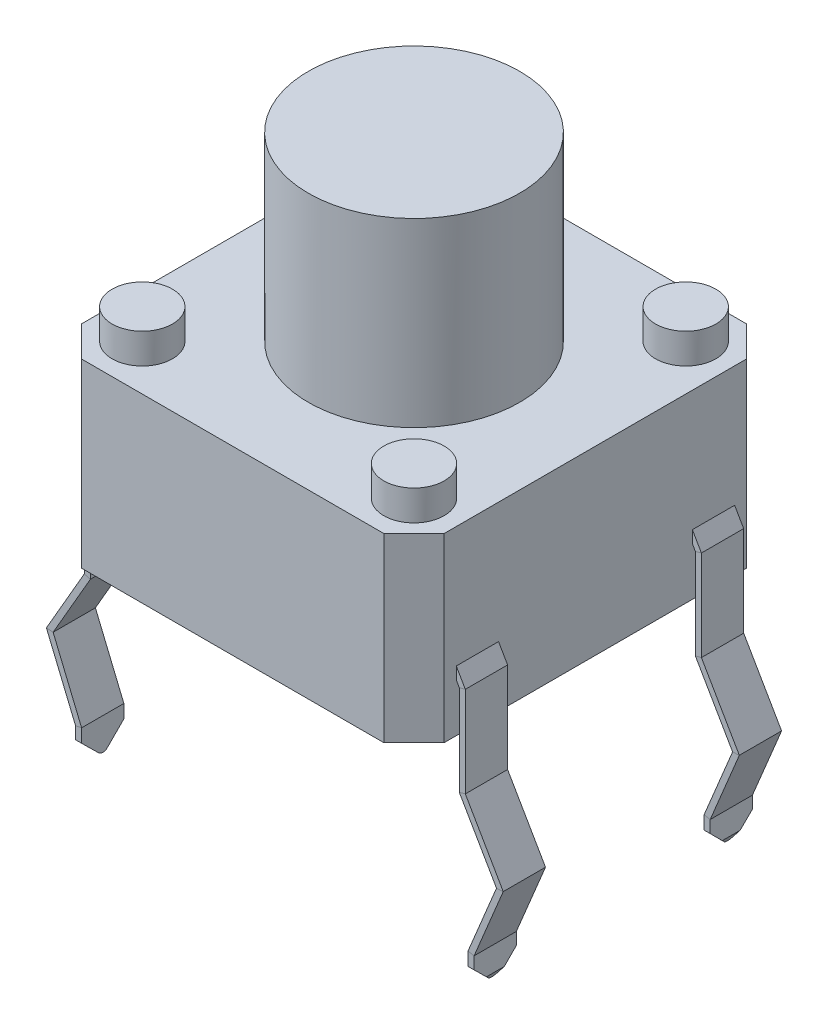
SolidWorks part; units mm, degrees
ref_plane "Front Plane" through (0, 0, 0) normal (0, 0, 1) x (1, 0, 0)
ref_plane "Top Plane" through (0, 0, 0) normal (0, 1, 0) x (1, 0, 0)
ref_plane "Right Plane" through (0, 0, 0) normal (1, 0, 0) x (0, 0, -1)
sketch "Sketch1" plane through (0, 0, 0) normal (0, 1, 0) x (1, 0, 0)
  line L1 (-3.005, -3.005) -> (3.005, -3.005)
  line L2 (-3.005, -3.005) -> (-3.005, 3.005)
  line L3 (-3.005, 3.005) -> (3.005, 3.005)
  line L4 (3.005, -3.005) -> (3.005, 3.005)
  line L5 (-3.005, -3.005) -> (3.005, 3.005) construction
  line L6 (-3.005, 3.005) -> (3.005, -3.005) construction
  point P0 (0, 0)
  dimension "D1" = 6.01
  dimension "D2" = 6.01
extrude "Boss-Extrude1" add sketch "Sketch1" along normal blind 3
chamfer "Chamfer1" distance 0.5 angle 45 4 edges at (3.005, 1.5, -3.005) (-3.005, 1.5, -3.005) (-3.005, 1.5, 3.005) (3.005, 1.5, 3.005)
sketch "Sketch3" plane through (0, 3, 0) normal (0, 1, 0) x (1, 0, 0)
  circle A0 centre (0, 0) radius 1.75
extrude "Boss-Extrude2" add sketch "Sketch3" along normal blind 3
sketch "Sketch4" plane through (0, 3, 0) normal (0, 1, 0) x (1, 0, 0)
  circle A0 centre (2.25, 2.25) radius 0.5
  circle A1 centre (2.25, -2.25) radius 0.5
  circle A2 centre (-2.25, 2.25) radius 0.5
sketch "Sketch5" plane through (0, 3, 0) normal (0, 1, 0) x (1, 0, 0)
  circle A0 centre (-2.25, -2.25) radius 0.5
extrude "Boss-Extrude6" add sketch "Sketch4" along normal blind 0.5
extrude "Boss-Extrude7" add sketch "Sketch5" along normal blind 0.5
sketch "Sketch6" plane through (-3.005, 0, 0) normal (-1, 0, 0) x (0, 0, 1)
  line L0 (-2.505, 0) -> (2.505, 0) construction
  line L1 (-2.305, 1) -> (-1.605, 1)
  line L2 (-2.305, 1) -> (-2.305, 0.8)
  line L3 (-2.305, 0.8) -> (-1.605, 0.8)
  line L4 (-1.605, 1) -> (-1.605, 0.8)
  line L5 (-2.305, 1) -> (-1.605, 0.8) construction
  line L6 (-2.305, 0.8) -> (-1.605, 1) construction
  line L7 (-2.505, 3) -> (-2.505, 0) construction
  point P0 (-1.955, 0.9)
  dimension "D1" = 0.7
  dimension "D2" = 0.2
  dimension "D3" = 1
  dimension "D4" = 0.2
sketch "Sketch7" plane through (0, 0, 0) normal (0, 0, 1) x (1, 0, 0)
  line L0 (-3.005, 0.9) -> (-3.105, 0.7268)
  line L1 (-3.105, 0.7268) -> (-3.105, -0.7732)
  line L2 (-3.105, -0.7732) -> (-3.7272, -1.8508)
  line L3 (-3.7272, -1.8508) -> (-3.25, -3)
  line L4 (-3.25, -3) -> (-3.25, -3.5)
  line L5 (2.505, 0) -> (-2.505, 0) construction
  line L6 (-3.005, 3) -> (-3.005, 0) construction
  dimension "D1" = 3.5
  dimension "D2" = 0.1
  dimension "D3" = 3.25
  dimension "D4" = 0.5
  dimension "D5" = 1.5
  dimension "D6" = 150
  dimension "D7" = 150
sweep "Sweep1" add profiles "Sketch6" path "Sketch7"
mirror "Mirror1" about plane through (0, 0, 0) normal (0, 0, 1) of "Sweep1"
mirror "Mirror2" about plane through (0, 0, 0) normal (1, 0, 0) of "Mirror1", "Sweep1"
sketch "Sketch8" plane through (0, 0, 0) normal (1, 0, 0) x (0, 0, -1)
  line L0 (-2.305, -3.2117) -> (-2.305, -3.5866)
  line L1 (-2.305, -3.01) -> (-2.305, -3.4134) construction
  line L2 (-2.305, -3.5866) -> (-1.605, -3.5866)
  line L3 (-1.605, -3.5866) -> (-1.605, -3.2117)
  line L4 (-1.605, -3.01) -> (-1.605, -3.4134) construction
  line L5 (-1.605, -3.2117) -> (-1.8817, -3.4893)
  line L6 (-2.0227, -3.4899) -> (-2.305, -3.2117)
  arc A0 (-1.8817, -3.4893) -> (-2.0227, -3.4899) centre (-1.9525, -3.4187) cw
  dimension "D1" = 0.1
extrude "Cut-Extrude1" cut sketch "Sketch8" against normal through all and the other way through all
mirror "Mirror3" about plane through (0, 0, 0) normal (0, 0, 1) of "Cut-Extrude1"
